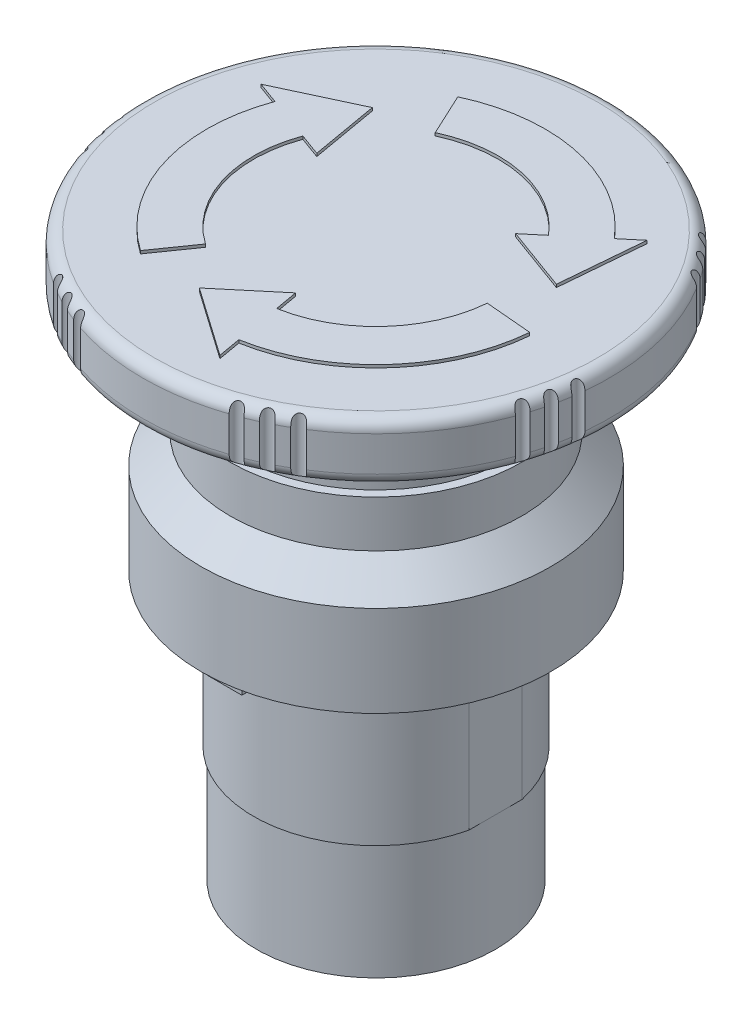
SolidWorks part; units mm, degrees
ref_plane "Front Plane" through (0, 0, 0) normal (0, 0, 1) x (1, 0, 0)
ref_plane "Top Plane" through (0, 0, 0) normal (0, 1, 0) x (1, 0, 0)
ref_plane "Right Plane" through (0, 0, 0) normal (1, 0, 0) x (0, 0, -1)
sketch "Sketch1" plane through (0, 0, 0) normal (0, 1, 0) x (1, 0, 0)
  circle A0 centre (0, 0) radius 15
  dimension "D1" = 30
extrude "Boss-Extrude1" add sketch "Sketch1" along normal blind 6.3
sketch "Sketch2" plane through (0, 6.3, 0) normal (0, 1, 0) x (1, 0, 0)
  circle A0 centre (0, 0) radius 15
  dimension "D1" = 30
extrude "Boss-Extrude2" add sketch "Sketch2" along normal blind 1.5
sketch "Sketch3" plane through (0, 7.8, 0) normal (0, 1, 0) x (1, 0, 0)
  circle A0 centre (0, 0) radius 15
  point P3 (0, 0)
  dimension "D1" = 30
extrude "Boss-Extrude3" add sketch "Sketch3" along normal blind 2.5 draft 45
sketch "Sketch4" plane through (0, 10.3, 0) normal (0, 1, 0) x (1, 0, 0)
  circle A0 centre (0, 0) radius 12.5
  dimension "D1" = 25
extrude "Boss-Extrude4" add sketch "Sketch4" along normal blind 4
sketch "Sketch5" plane through (0, 14.3, 0) normal (0, 1, 0) x (1, 0, 0)
  circle A0 centre (0, 0) radius 11.75
  dimension "D1" = 23.5
extrude "Cut-Extrude1" cut sketch "Sketch5" against normal blind 14
sketch "Sketch6" plane through (0, 0.3, 0) normal (0, 1, 0) x (1, 0, 0)
  circle A0 centre (0, 0) radius 11.25
  dimension "D1" = 22.5
extrude "Boss-Extrude5" add sketch "Sketch6" along normal blind 20
sketch "Sketch8" plane through (0, 20.3, 0) normal (0, 1, 0) x (1, 0, 0)
  circle A0 centre (0, 0) radius 20
  dimension "D1" = 40
extrude "Boss-Extrude7" add sketch "Sketch8" along normal blind 5
fillet "Fillet1" radius 1 2 edges at (0, 25.3, 20) (0, 20.3, 20)
sketch "Sketch9" plane through (0, 25.3, 0) normal (0, 1, 0) x (1, 0, 0)
  line L0 (0, 0) -> (0, 20.0473) construction
  line L1 (0, 0) -> (2, 19.9472) construction
  circle A0 centre (0, 0) radius 20.0473 construction
  circle A1 centre (2, 19.9472) radius 0.5
  circle A2 centre (0, 20.0473) radius 0.5
  circle A3 centre (-2, 19.9472) radius 0.5
  circle A4 centre (16.8424, 10.8732) radius 0.5
  circle A5 centre (15.6736, 12.4993) radius 0.5
  circle A6 centre (14.3484, 14.0006) radius 0.5
  circle A7 centre (19.0021, -6.3885) radius 0.5
  circle A8 centre (19.5446, -4.4609) radius 0.5
  circle A9 centre (19.8922, -2.4888) radius 0.5
  circle A10 centre (6.8528, -18.8396) radius 0.5
  circle A11 centre (8.6982, -18.062) radius 0.5
  circle A12 centre (10.4567, -17.1041) radius 0.5
  circle A13 centre (-10.4567, -17.1041) radius 0.5
  circle A14 centre (-8.6982, -18.062) radius 0.5
  circle A15 centre (-6.8528, -18.8396) radius 0.5
  circle A16 centre (-19.8922, -2.4888) radius 0.5
  circle A17 centre (-19.5446, -4.4609) radius 0.5
  circle A18 centre (-19.0021, -6.3885) radius 0.5
  circle A19 centre (-14.3484, 14.0006) radius 0.5
  circle A20 centre (-15.6736, 12.4993) radius 0.5
  circle A21 centre (-16.8424, 10.8732) radius 0.5
  point P48 (0, 0)
  dimension "D1" = 1
  dimension "D2" = 1
  dimension "D3" = 2
  dimension "D4" = 7
extrude "Cut-Extrude2" cut sketch "Sketch9" against normal blind 15
sketch "Sketch10" plane through (0, 25.3, 0) normal (0, 1, 0) x (1, 0, 0)
  line L0 (0, 0) -> (14.5548, 12.213) construction
  line L1 (0, 0) -> (0, 19) construction
  line L2 (11.1076, 9.3204) -> (12.6397, 10.606)
  line L3 (12.6397, 10.606) -> (12.0139, 3.4521)
  line L4 (12.0139, 3.4521) -> (6.5114, 5.4637)
  line L5 (6.5114, 5.4637) -> (8.0435, 6.7493)
  line L6 (0, 0) -> (-8.0297, 17.2198) construction
  line L7 (-6.128, 13.1415) -> (-4.4375, 9.5162)
  line L8 (14.4448, -1.2638) -> (10.46, -0.9151)
  line L9 (1.476, -8.3709) -> (1.8233, -10.3405)
  line L10 (-3.0173, -12.1304) -> (1.476, -8.3709)
  line L11 (2.8652, -16.2493) -> (-3.0173, -12.1304)
  line L12 (2.5179, -14.2797) -> (2.8652, -16.2493)
  line L13 (-8.3169, -11.8777) -> (-6.0226, -8.6011)
  line L14 (-7.9874, 2.9072) -> (-9.8668, 3.5912)
  line L15 (-8.9966, 8.6782) -> (-7.9874, 2.9072)
  line L16 (-15.5049, 5.6433) -> (-8.9966, 8.6782)
  line L17 (-13.6255, 4.9593) -> (-15.5049, 5.6433)
  arc A0 (11.1076, 9.3204) -> (-6.128, 13.1415) centre (0, 0) ccw
  arc A1 (8.0435, 6.7493) -> (-4.4375, 9.5162) centre (0, 0) ccw
  arc A2 (12.0139, 3.4521) -> (-5.2827, 11.3288) centre (0, 0) ccw
  circle A3 centre (0, 0) radius 19 construction
  arc A4 (1.8233, -10.3405) -> (10.46, -0.9151) centre (0, 0) ccw
  arc A5 (2.5179, -14.2797) -> (14.4448, -1.2638) centre (0, 0) ccw
  arc A6 (-9.8668, 3.5912) -> (-6.0226, -8.6011) centre (0, 0) ccw
  arc A7 (-13.6255, 4.9593) -> (-8.3169, -11.8777) centre (0, 0) ccw
  point P33 (0, 0)
  dimension "D1" = 29
  dimension "D2" = 21
  dimension "D3" = 25
  dimension "D4" = 50
  dimension "D5" = 2
  dimension "D6" = 45
  dimension "D7" = 25
  dimension "D8" = 3
extrude "Boss-Extrude8" add sketch "Sketch10" along normal blind 0.25 contours L17 A7 L13 A6 L14 L15 L16 | L4 A2 L7 A1 L5 | A2 L3 L2 A0 L7 | L12 A5 L8 A4 L9 L10 L11
sketch "Sketch12" plane through (0, 0, 0) normal (0, -1, 0) x (1, 0, 0)
  line L0 (0, 0) -> (0, 0.2954) construction
  line L1 (0, 15) -> (0, 0) construction
  line L4 (1.5, 10.8972) -> (1.5, 13)
  line L5 (1.5, 13) -> (-1.5, 13)
  line L6 (-1.5, 10.8972) -> (-1.5, 13)
  arc A0 (-1.5, 10.8972) -> (1.5, 10.8972) centre (0, 0) ccw
  circle A1 centre (0, 0) radius 15 construction
  dimension "D1" = 22
  dimension "D2" = 3
  dimension "D3" = 1.5
  dimension "D4" = 13
extrude "Boss-Extrude9" add sketch "Sketch12" along normal blind 2
sketch "Sketch13" plane through (0, -2, 0) normal (0, -1, 0) x (1, 0, 0)
  circle A0 centre (0, 0) radius 10.5
  arc A1 (-1.5, 10.8972) -> (1.5, 10.8972) centre (0, 0) ccw construction
  dimension "D1" = 0.5
extrude "Boss-Extrude10" add sketch "Sketch13" along normal blind 11
sketch "Sketch14" plane through (0, -13, 0) normal (0, -1, 0) x (1, 0, 0)
  circle A0 centre (0, 0) radius 10.25
  dimension "D1" = 20.5
extrude "Boss-Extrude11" add sketch "Sketch14" along normal blind 10
sketch "Sketch15" plane through (0, -23, 0) normal (0, -1, 0) x (1, 0, 0)
  line L1 (-10.25, 15) -> (-20.25, 15)
  line L2 (-10.25, 15) -> (-10.25, -15)
  line L3 (-10.25, -15) -> (-20.25, -15)
  line L4 (-20.25, 15) -> (-20.25, -15)
  line L5 (10.25, 15.998) -> (20.25, 15.998)
  line L6 (10.25, 15.998) -> (10.25, -14.002)
  line L7 (10.25, -14.002) -> (20.25, -14.002)
  line L8 (20.25, 15.998) -> (20.25, -14.002)
  circle A0 centre (0, 0) radius 19 construction
  circle A1 centre (0, 0) radius 10.25 construction
  dimension "D1" = 10
  dimension "D2" = 30
  dimension "D3" = 15
extrude "Cut-Extrude3" cut sketch "Sketch15" against normal up to surface (21 mm away) up to face at (0, -2, 6.4743)
